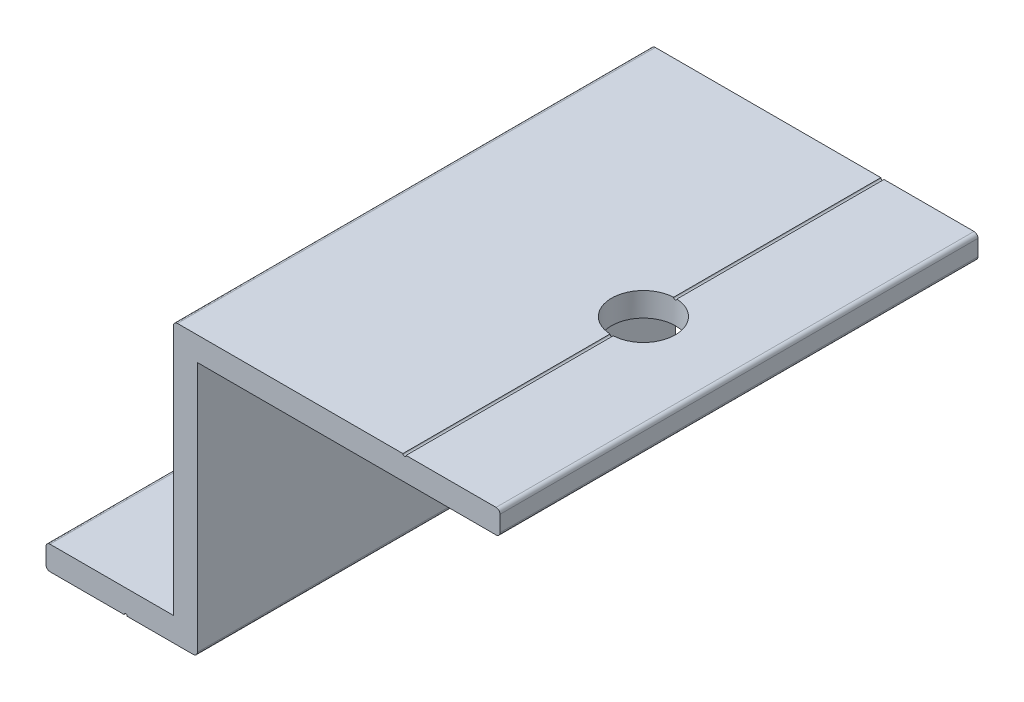
SolidWorks part; units mm, degrees
material "6061 合金"
ref_plane "前视基准面" through (0, 0, 0) normal (0, 0, 1) x (1, 0, 0)
ref_plane "上视基准面" through (0, 0, 0) normal (0, 1, 0) x (1, 0, 0)
ref_plane "右视基准面" through (0, 0, 0) normal (1, 0, 0) x (0, 0, -1)
sketch "草图1" plane through (0, 0, 0) normal (0, 0, 1) x (1, 0, 0)
  line L0 (-0.0558, 0) -> (0.0667, 0) construction
  line L1 (0, 0.0417) -> (0, -0.0417) construction
  line L2 (0, 0) -> (19, 0)
  line L3 (0, 0) -> (0, 3)
  line L4 (0, 3) -> (16, 3)
  line L5 (16, 3) -> (16, 35)
  line L6 (16, 35) -> (57, 35)
  line L7 (57, 35) -> (57, 32)
  line L8 (57, 32) -> (19, 32)
  line L9 (19, 32) -> (19, 0)
  dimension "D1" = 38
  dimension "D2" = 19
  dimension "D3" = 32
  dimension "D4" = 3
  dimension "D5" = 3
  dimension "D6" = 3
extrude "凸台-拉伸1" add sketch "草图1" along normal blind 60
sketch "草图2" plane through (0, 35, 0) normal (0, 1, 0) x (1, 0, 0)
  line L0 (57, -60) -> (16, -60) construction
  line L2 (0, -60) -> (0, 0) construction
  line L5 (10, -3.1264) -> (10, -85.6161) construction
  line L6 (16, -60) -> (16, 0) construction
  circle A0 centre (45, -30) radius 4
  circle A1 centre (10, -30) radius 2.1
  circle A2 centre (10, -50) radius 2.1
  circle A3 centre (10, -10) radius 2.1
  dimension "D1" = 10
  dimension "D3" = 8
  dimension "D4" = 4.2
  dimension "D6" = 20
  dimension "D8" = 4.2
  dimension "D9" = 4.2
  dimension "D2" = 30
  dimension "D5" = 29
  dimension "D7" = 20
extrude "切除-拉伸1" cut sketch "草图2" against normal through all
sketch "草图3" plane through (0, 0, 60) normal (0, 0, 1) x (1, 0, 0)
  line L2 (0, 0) -> (19, 0) construction
  line L3 (0, 3) -> (0, 0) construction
  line L7 (57, 35) -> (16, 35) construction
  line L8 (19, 0) -> (19, 32) construction
  circle A1 centre (10, 0) radius 0.2
  circle A3 centre (45, 35) radius 0.2
  dimension "D1" = 10
  dimension "D2" = 0.4
  dimension "D3" = 26
  dimension "D4" = 0.4
extrude "切除-拉伸2" cut sketch "草图3" against normal blind 70
fillet "圆角1" radius 0.5 6 edges at (57, 32, 30) (57, 35, 30) (16, 35, 30) (19, 0, 30) (0, 0, 30) (0, 3, 30)
